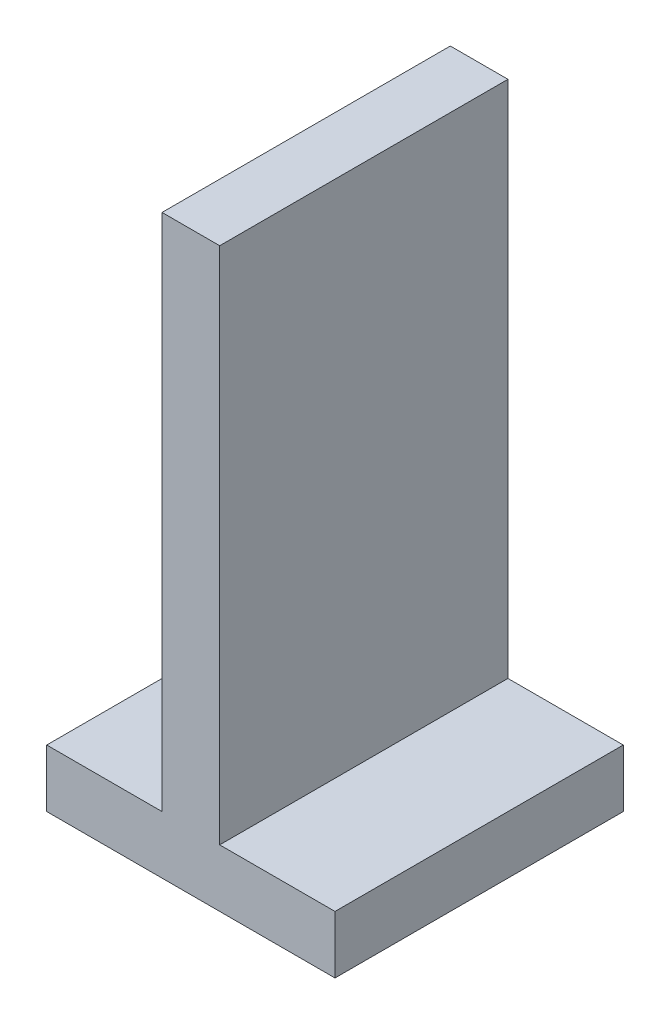
SolidWorks part; units mm, degrees
ref_plane "Plan de face" through (0, 0, 0) normal (0, 0, 1) x (1, 0, 0)
ref_plane "Plan de dessus" through (0, 0, 0) normal (0, 1, 0) x (1, 0, 0)
ref_plane "Plan de droite" through (0, 0, 0) normal (1, 0, 0) x (0, 0, -1)
sketch "Esquisse1" plane through (0, 0, 0) normal (0, 0, 1) x (1, 0, 0)
  line L0 (0, 0) -> (500, 0)
  line L1 (500, 0) -> (500, 100)
  line L2 (500, 100) -> (300, 100)
  line L3 (300, 100) -> (300, 1000)
  line L4 (300, 1000) -> (200, 1000)
  line L5 (200, 1000) -> (200, 100)
  line L6 (200, 100) -> (0, 100)
  line L7 (0, 100) -> (0, 0)
  dimension "D1" = 500
  dimension "D2" = 1000
  dimension "D3" = 100
  dimension "D4" = 100
  dimension "D5" = 200
  dimension "D6" = 200
extrude "Boss.-Extru.1" add sketch "Esquisse1" along normal blind 500
sketch "Esquisse4" plane through (0, 100, 0) normal (0, 1, 0) x (1, 0, 0)
  line L0 (200, -80) -> (200, -130)
  line L1 (200, -500) -> (200, 0) construction
  line L2 (200, -130) -> (190, -130)
  line L3 (190, -130) -> (190, -100)
  line L4 (190, -100) -> (185, -100)
  line L5 (185, -100) -> (185, -130)
  line L6 (185, -130) -> (175, -130)
  line L7 (175, -130) -> (175, -80)
  line L8 (175, -80) -> (200, -80)
  line L9 (200, 0) -> (0, 0) construction
  line L10 (500, -250) -> (-33.1915, -250) construction
  line L11 (500, -500) -> (500, 0) construction
  line L12 (175, -370) -> (175, -420)
  line L13 (185, -370) -> (175, -370)
  line L14 (185, -400) -> (185, -370)
  line L15 (190, -400) -> (185, -400)
  line L16 (190, -370) -> (190, -400)
  line L17 (200, -370) -> (190, -370)
  line L18 (200, -420) -> (200, -370)
  line L19 (175, -420) -> (200, -420)
  dimension "D1" = 50
  dimension "D2" = 50
  dimension "D3" = 80
  dimension "D4" = 25
  dimension "D5" = 30
  dimension "D6" = 10
  dimension "D7" = 10
  dimension "D8" = 300
extrude "Boss.-Extru.3" add sketch "Esquisse4" along normal blind 600
